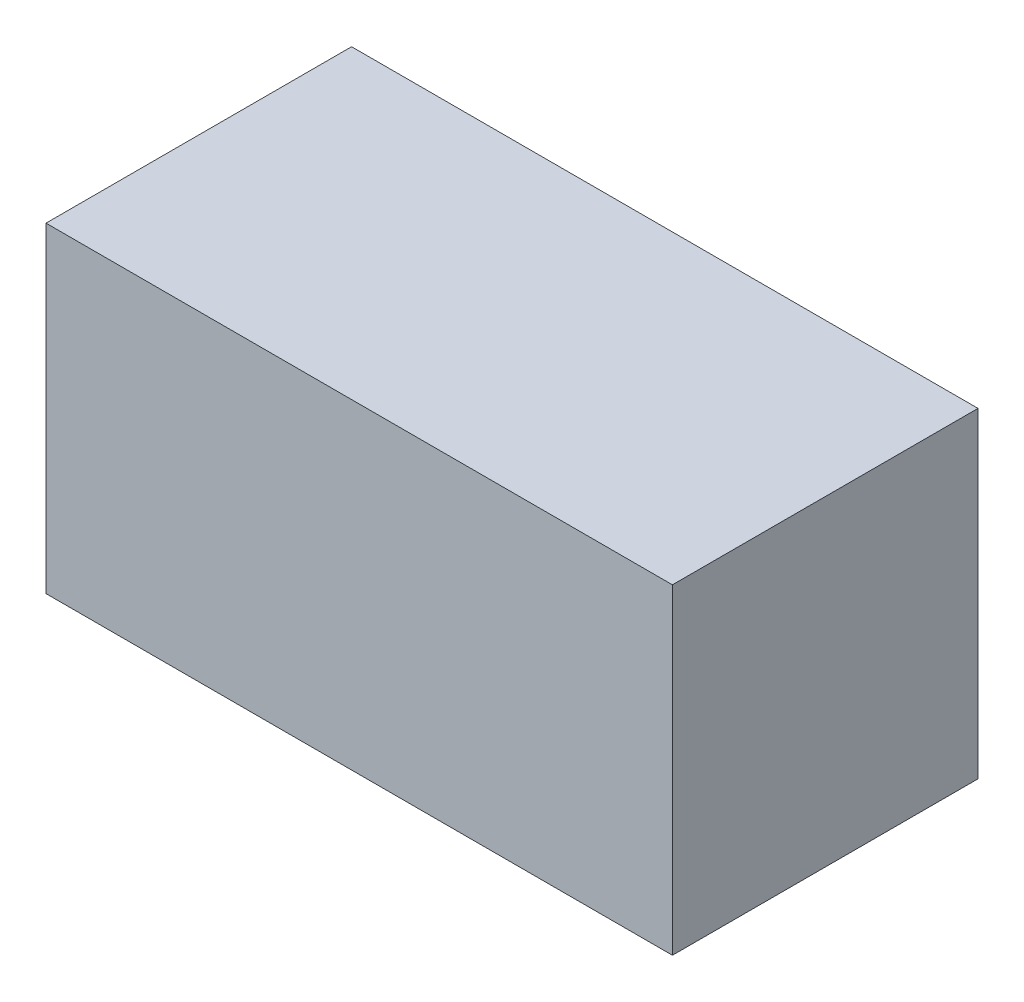
SolidWorks part; units mm, degrees
ref_plane "Front Plane" through (0, 0, 0) normal (0, 0, 1) x (1, 0, 0)
ref_plane "Top Plane" through (0, 0, 0) normal (0, 1, 0) x (1, 0, 0)
ref_plane "Right Plane" through (0, 0, 0) normal (1, 0, 0) x (0, 0, -1)
sketch "Sketch1" plane through (0, 0, 0) normal (0, 0, 1) x (1, 0, 0)
  line L1 (0, 0) -> (41, 0)
  line L2 (0, 0) -> (0, 21)
  line L3 (0, 21) -> (41, 21)
  line L4 (41, 0) -> (41, 21)
  dimension "D1" = 21
  dimension "D2" = 41
extrude "Boss-Extrude1" add sketch "Sketch1" along normal blind 20
